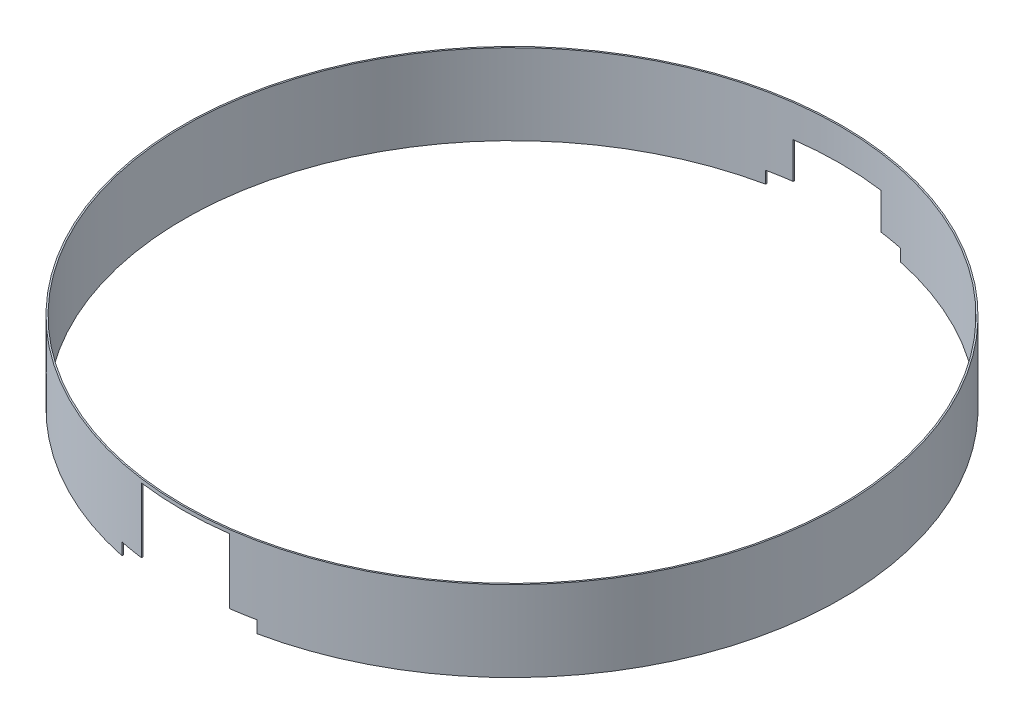
SolidWorks part; units mm, degrees
ref_plane "Front Plane" through (0, 0, 0) normal (0, 0, 1) x (1, 0, 0)
ref_plane "Top Plane" through (0, 0, 0) normal (0, 1, 0) x (1, 0, 0)
ref_plane "Right Plane" through (0, 0, 0) normal (1, 0, 0) x (0, 0, -1)
sketch "Croquis1" plane through (0, 0, 0) normal (0, 1, 0) x (1, 0, 0)
  circle A0 centre (0, 0) radius 450
  circle A1 centre (0, 0) radius 448
  dimension "D1" = 900
  dimension "D2" = 2
extrude "Saliente-Extruir2" add sketch "Croquis1" along normal blind 110
sketch "Croquis2" plane through (0, 0, 0) normal (0, 0, 1) x (1, 0, 0)
  line L0 (448, 110) -> (-448, 110) construction
  line L1 (-60, 105) -> (60, 105)
  line L2 (-60, 105) -> (-60, -105)
  line L3 (-60, -105) -> (60, -105)
  line L4 (60, 105) -> (60, -105)
  line L5 (-60, 105) -> (60, -105) construction
  line L6 (-60, -105) -> (60, 105) construction
  line L7 (-60, 0) -> (-92, 0)
  line L8 (-60, 0) -> (-60, 16.5)
  line L9 (-60, 16.5) -> (-92, 16.5)
  line L10 (-92, 0) -> (-92, 16.5)
  line L11 (60, 0) -> (92, 0)
  line L12 (60, 0) -> (60, 16.5)
  line L13 (60, 16.5) -> (92, 16.5)
  line L14 (92, 0) -> (92, 16.5)
  point P0 (0, 0)
  dimension "D1" = 120
  dimension "D2" = 32
  dimension "D3" = 16.5
  dimension "D4" = 32
  dimension "D5" = 16.5
  dimension "D6" = 5
extrude "Cortar-Extruir2" cut sketch "Croquis2" along normal blind 500 contours L4 L1 L2 L3 | L10 L7 L2 L9 | L14 L13 L12 L11
sketch "Croquis3" plane through (0, 0, 0) normal (0, 0, 1) x (1, 0, 0)
  line L0 (-60, 105) -> (-60, -105) construction
  line L1 (60, 0) -> (-60, 0)
  line L2 (60, 0) -> (60, 66)
  line L3 (60, 66) -> (-60, 66)
  line L4 (-60, 0) -> (-60, 66)
  line L6 (-60, 0) -> (-92, 0)
  line L7 (-60, 0) -> (-60, 16.5)
  line L8 (-60, 16.5) -> (-92, 16.5)
  line L9 (-92, 0) -> (-92, 16.5)
  line L10 (60, 0) -> (92, 0)
  line L11 (60, 0) -> (60, 16.5)
  line L12 (60, 16.5) -> (92, 16.5)
  line L13 (92, 0) -> (92, 16.5)
  dimension "D1" = 66
extrude "Cortar-Extruir3" cut sketch "Croquis3" against normal blind 500 contours L4 L1 L2 L3 | L10 L13 L12 L2 | L9 L6 L4 L8
